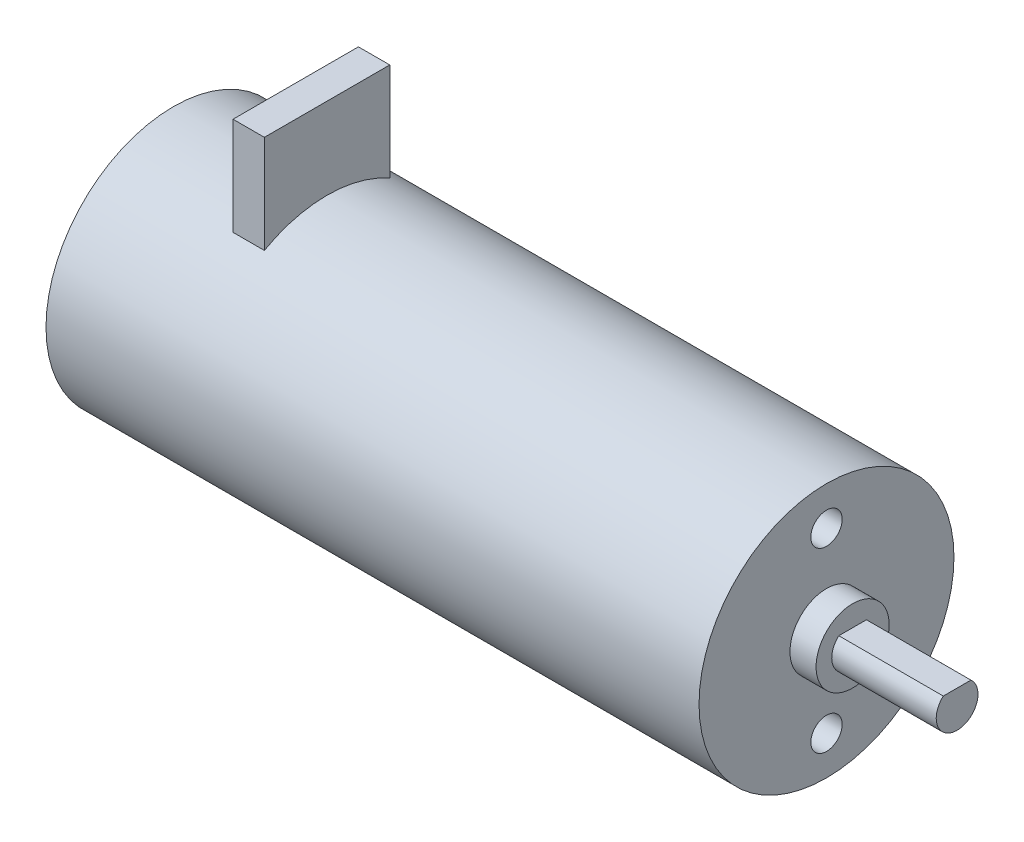
SolidWorks part; units mm, degrees
ref_plane "Front Plane" through (0, 0, 0) normal (0, 0, 1) x (1, 0, 0)
ref_plane "Top Plane" through (0, 0, 0) normal (0, 1, 0) x (1, 0, 0)
ref_plane "Right Plane" through (0, 0, 0) normal (1, 0, 0) x (0, 0, -1)
sketch "Sketch1" plane through (0, 0, 0) normal (1, 0, 0) x (0, 0, -1)
  circle A0 centre (0, 0) radius 12.2
  dimension "D1" = 24.4
extrude "Boss-Extrude1" add sketch "Sketch1" along normal blind 62.5
sketch "Sketch2" plane through (62.5, 0, 0) normal (1, 0, 0) x (0, 0, -1)
  circle A0 centre (0, 0) radius 3.5
  dimension "D1" = 7
extrude "Boss-Extrude2" add sketch "Sketch2" along normal blind 2.5
sketch "Sketch3" plane through (65, 0, 0) normal (1, 0, 0) x (0, 0, -1)
  line L0 (-1.3229, 1.5) -> (1.3229, 1.5)
  arc A0 (-1.3229, 1.5) -> (1.3229, 1.5) centre (0, 0) ccw
  dimension "D1" = 4
  dimension "D2" = 1.5
extrude "Boss-Extrude3" add sketch "Sketch3" along normal blind 10
sketch "Sketch4" plane through (62.5, 0, 0) normal (1, 0, 0) x (0, 0, -1)
  line L0 (0, 0) -> (13.2707, 0) construction
  circle A0 centre (0, 8.5) radius 1.5
  circle A1 centre (0, -8.5) radius 1.5
  dimension "D1" = 3
  dimension "D2" = 8.5
extrude "Cut-Extrude1" cut sketch "Sketch4" against normal blind 5
sketch "Sketch5" plane through (0, 0, 0) normal (0, 1, 0) x (1, 0, 0)
  line L0 (0, 12.2) -> (0, -12.2) construction
  line L1 (11.7, 6) -> (14.7, 6)
  line L2 (11.7, 6) -> (11.7, -6)
  line L3 (11.7, -6) -> (14.7, -6)
  line L4 (14.7, 6) -> (14.7, -6)
  dimension "D1" = 14.7
  dimension "D2" = 6
  dimension "D3" = 6
  dimension "D4" = 3
extrude "Boss-Extrude4" add sketch "Sketch5" along normal blind 20
equation "\"D1@Boss-Extrude1\"=17+30.8+14.7"
